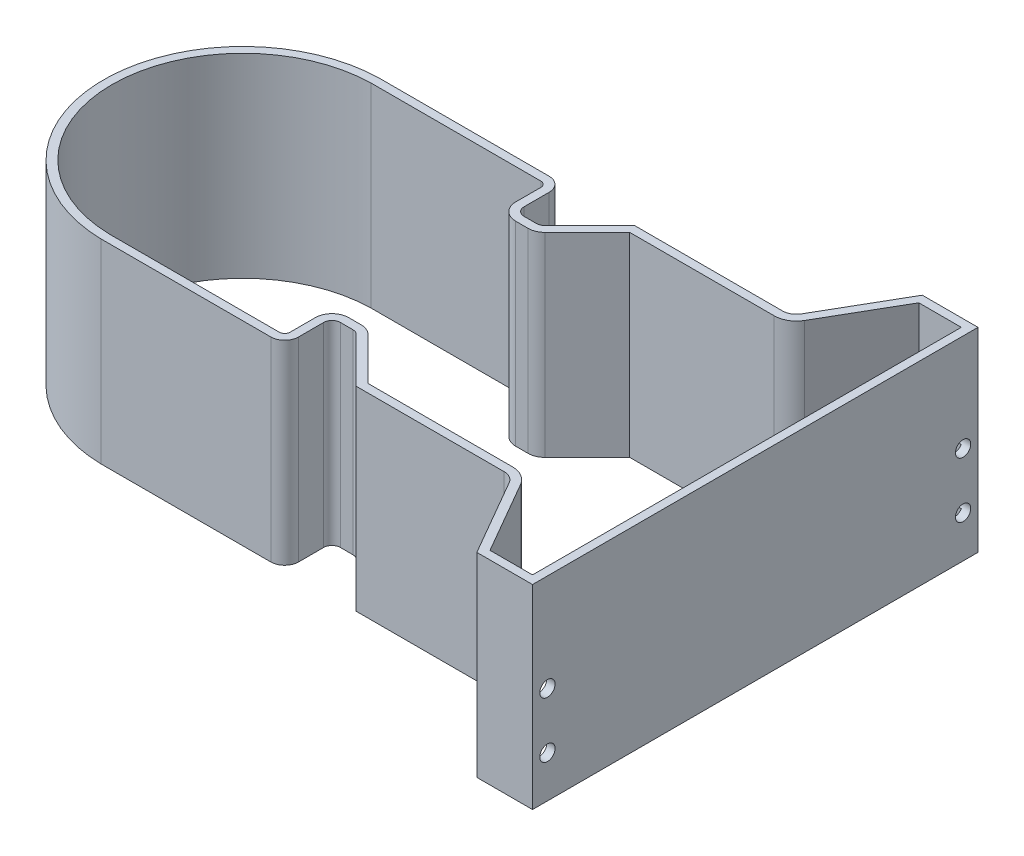
SolidWorks part; units mm, degrees
ref_plane "Front Plane" through (0, 0, 0) normal (0, 0, 1) x (1, 0, 0)
ref_plane "Top Plane" through (0, 0, 0) normal (0, 1, 0) x (1, 0, 0)
ref_plane "Right Plane" through (0, 0, 0) normal (1, 0, 0) x (0, 0, -1)
sketch "Sketch1" plane through (0, 0, 0) normal (0, 1, 0) x (1, 0, 0)
  line L0 (15.2546, 44.9902) -> (15.2546, 35.9902)
  line L1 (-50.7454, -49.9902) -> (10.2546, -49.9902)
  line L3 (-50.7454, 49.9902) -> (10.2546, 49.9902)
  line L5 (-50.7454, -49.9902) -> (50.7454, 49.9902) construction
  line L6 (-50.7454, 49.9902) -> (50.7454, -49.9902) construction
  line L7 (18.2546, 32.9902) -> (22.7119, 32.9902)
  line L8 (24.8333, 33.8689) -> (40.9546, 49.9902)
  line L9 (40.9546, 49.9902) -> (94.0678, 49.9902)
  line L10 (98.398, 52.4902) -> (114.2807, 80)
  line L11 (114.2807, 80) -> (134.2807, 80)
  line L12 (-49.7577, 0) -> (134.2807, 0) construction
  line L13 (134.2807, 80) -> (134.2807, -80)
  line L14 (40.9546, 49.9902) -> (96.9546, 49.9902)
  line L15 (40.9546, 49.9902) -> (50.7454, 49.9902)
  line L17 (114.2807, -80) -> (134.2807, -80)
  line L18 (98.398, -52.4902) -> (114.2807, -80)
  line L19 (40.9546, -49.9902) -> (94.0678, -49.9902)
  line L20 (18.2546, -32.9902) -> (22.7119, -32.9902)
  line L21 (24.8333, -33.8689) -> (40.9546, -49.9902)
  line L22 (15.2546, -44.9902) -> (15.2546, -35.9902)
  line L23 (40.9546, -49.9902) -> (50.7454, -49.9902)
  arc A0 (-50.7454, 49.9902) -> (-50.7454, -49.9902) centre (-49.7577, 0) ccw
  arc A1 (22.7119, 32.9902) -> (24.8333, 33.8689) centre (22.7119, 35.9902) ccw
  arc A2 (18.2546, 32.9902) -> (15.2546, 35.9902) centre (18.2546, 35.9902) cw
  arc A3 (15.2546, 44.9902) -> (10.2546, 49.9902) centre (10.2546, 44.9902) ccw
  arc A4 (15.2546, -44.9902) -> (10.2546, -49.9902) centre (10.2546, -44.9902) cw
  arc A5 (22.7119, -32.9902) -> (24.8333, -33.8689) centre (22.7119, -35.9902) cw
  arc A6 (18.2546, -32.9902) -> (15.2546, -35.9902) centre (18.2546, -35.9902) ccw
  arc A7 (98.398, -52.4902) -> (94.0678, -49.9902) centre (94.0678, -54.9902) ccw
  arc A8 (98.398, 52.4902) -> (94.0678, 49.9902) centre (94.0678, 54.9902) cw
  point P0 (0, 0)
  point P24 (23.9546, 32.9902)
  point P27 (15.2546, 32.9902)
  point P30 (15.2546, 49.9902)
  point P33 (15.2546, -49.9902)
  point P37 (23.9546, -32.9902)
  point P40 (15.2546, -32.9902)
  point P43 (96.9546, -49.9902)
  dimension "D2" = 100
  dimension "D11" = 3
  dimension "D12" = 5
  dimension "D13" = 5
  dimension "D14" = 3
  dimension "D15" = 5
  dimension "D1" = 120
  dimension "D3" = 8.7
  dimension "D4" = 135
  dimension "D5" = 17
  dimension "D6" = 56
  dimension "D7" = 160
  dimension "D8" = 20
  dimension "D10" = 66
extrude "Boss-Extrude1" add sketch "Sketch1" along normal blind 70
sketch "Sketch3" plane through (134.2807, 0, 0) normal (1, 0, 0) x (0, 0, -1)
  line L0 (-80, 70) -> (80, 0) construction
  line L1 (-80, 0) -> (80, 70) construction
  line L2 (0, 35) -> (-72.6822, 35) construction
  line L3 (-74.647, 35) -> (-74.647, 15) construction
  line L4 (0, 35) -> (0, 70) construction
  line L5 (80, 70) -> (-80, 70) construction
  line L6 (0, 35) -> (-80, 35) construction
  line L7 (-80, 70) -> (80, 70)
  line L8 (-80, 70) -> (-80, 0)
  line L9 (-80, 0) -> (80, 0)
  line L10 (80, 70) -> (80, 0)
  line L11 (-80, 70) -> (80, 0) construction
  line L12 (-80, 0) -> (80, 70) construction
  line L13 (74.647, 35) -> (74.647, 15) construction
  circle A0 centre (-74.647, 15) radius 2.75
  circle A1 centre (-74.647, 35) radius 2.75
  circle A17 centre (74.647, 35) radius 2.75
  circle A18 centre (74.647, 15) radius 2.75
  dimension "D1" = 20
sketch "Sketch5" plane through (0, 70, 0) normal (0, 1, 0) x (1, 0, 0)
  line L30 (116.0128, 77) -> (100.996, 50.9902)
  line L31 (94.0678, 46.9902) -> (42.1972, 46.9902)
  line L32 (42.1972, 46.9902) -> (26.9546, 31.7476)
  line L33 (22.7119, 29.9902) -> (18.2546, 29.9902)
  line L34 (12.2546, 35.9902) -> (12.2546, 44.9902)
  line L35 (10.2546, 46.9902) -> (-50.7153, 46.9902)
  line L36 (-50.7153, -46.9902) -> (10.2546, -46.9902)
  line L37 (12.2546, -44.9902) -> (12.2546, -35.9902)
  line L38 (18.2546, -29.9902) -> (22.7119, -29.9902)
  line L39 (26.9546, -31.7476) -> (42.1972, -46.9902)
  line L40 (42.1972, -46.9902) -> (94.0678, -46.9902)
  line L41 (100.996, -50.9902) -> (116.0128, -77)
  line L42 (116.0128, -77) -> (131.2807, -77)
  line L43 (131.2807, -77) -> (131.2807, 77)
  line L44 (131.2807, 77) -> (116.0128, 77)
  line L45 (116.0128, 77) -> (100.996, 50.9902)
  line L46 (94.0678, 46.9902) -> (42.1972, 46.9902)
  line L47 (42.1972, 46.9902) -> (26.9546, 31.7476)
  line L48 (22.7119, 29.9902) -> (18.2546, 29.9902)
  line L49 (12.2546, 35.9902) -> (12.2546, 44.9902)
  line L50 (10.2546, 46.9902) -> (-50.7153, 46.9902)
  line L51 (-50.7153, -46.9902) -> (10.2546, -46.9902)
  line L52 (12.2546, -44.9902) -> (12.2546, -35.9902)
  line L53 (18.2546, -29.9902) -> (22.7119, -29.9902)
  line L54 (26.9546, -31.7476) -> (42.1972, -46.9902)
  line L55 (42.1972, -46.9902) -> (94.0678, -46.9902)
  line L56 (100.996, -50.9902) -> (116.0128, -77)
  line L57 (116.0128, -77) -> (131.2807, -77)
  line L58 (131.2807, -77) -> (131.2807, 77)
  line L59 (131.2807, 77) -> (116.0128, 77)
  arc A18 (94.0678, 46.9902) -> (100.996, 50.9902) centre (94.0678, 54.9902) ccw
  arc A19 (22.7119, 29.9902) -> (26.9546, 31.7476) centre (22.7119, 35.9902) ccw
  arc A20 (12.2546, 35.9902) -> (18.2546, 29.9902) centre (18.2546, 35.9902) ccw
  arc A21 (-50.7153, 46.9902) -> (-50.7153, -46.9902) centre (-49.7577, 0) ccw
  arc A22 (18.2546, -29.9902) -> (12.2546, -35.9902) centre (18.2546, -35.9902) ccw
  arc A23 (26.9546, -31.7476) -> (22.7119, -29.9902) centre (22.7119, -35.9902) ccw
  arc A24 (100.996, -50.9902) -> (94.0678, -46.9902) centre (94.0678, -54.9902) ccw
  arc A25 (94.0678, 46.9902) -> (100.996, 50.9902) centre (94.0678, 54.9902) ccw
  arc A26 (22.7119, 29.9902) -> (26.9546, 31.7476) centre (22.7119, 35.9902) ccw
  arc A27 (12.2546, 35.9902) -> (18.2546, 29.9902) centre (18.2546, 35.9902) ccw
  arc A28 (-50.7153, 46.9902) -> (-50.7153, -46.9902) centre (-49.7577, 0) ccw
  arc A29 (18.2546, -29.9902) -> (12.2546, -35.9902) centre (18.2546, -35.9902) ccw
  arc A30 (26.9546, -31.7476) -> (22.7119, -29.9902) centre (22.7119, -35.9902) ccw
  arc A31 (100.996, -50.9902) -> (94.0678, -46.9902) centre (94.0678, -54.9902) ccw
  arc A32 (12.2546, 44.9902) -> (10.2546, 46.9902) centre (10.2546, 44.9902) ccw
  arc A33 (12.2546, 44.9902) -> (10.2546, 46.9902) centre (10.2546, 44.9902) ccw
  arc A34 (10.2546, -46.9902) -> (12.2546, -44.9902) centre (10.2546, -44.9902) ccw
  arc A35 (10.2546, -46.9902) -> (12.2546, -44.9902) centre (10.2546, -44.9902) ccw
  dimension "D1" = 3
extrude "Cut-Extrude3" cut sketch "Sketch5" against normal blind 70
extrude "Cut-Extrude6" cut sketch "Sketch3" against normal blind 5 contours A1 | A0 | A17 | A18
